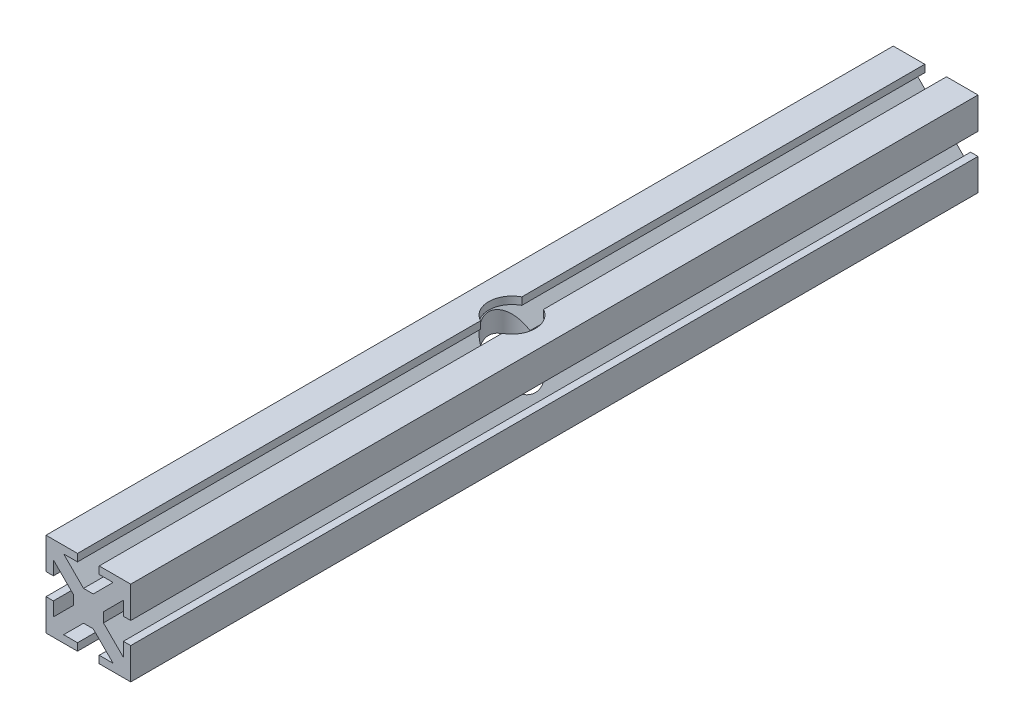
SolidWorks part; units mm, degrees
ref_plane "Front Plane" through (0, 0, 0) normal (0, 0, 1) x (1, 0, 0)
ref_plane "Top Plane" through (0, 0, 0) normal (0, 1, 0) x (1, 0, 0)
ref_plane "Right Plane" through (0, 0, 0) normal (1, 0, 0) x (0, 0, -1)
sketch "Sketch1" plane through (0, 0, 0) normal (0, 0, 1) x (1, 0, 0)
  line L1 (-12.7, -12.7) -> (12.7, -12.7)
  line L2 (-12.7, -12.7) -> (-12.7, 12.7)
  line L3 (-12.7, 12.7) -> (12.7, 12.7)
  line L4 (12.7, -12.7) -> (12.7, 12.7)
  line L5 (-12.7, -12.7) -> (12.7, 12.7) construction
  line L6 (-12.7, 12.7) -> (12.7, -12.7) construction
  point P0 (0, 0)
extrude "Boss-Extrude2" add sketch "Sketch1" along normal blind 254 contours L3 L4 L1 L2
sketch "Sketch3" plane through (0, 0, 254) normal (0, 0, 1) x (1, 0, 0)
  line L0 (-4.5212, 4.5212) -> (-12.7, 12.7)
  line L1 (-4.5212, 4.5212) -> (4.5212, 4.5212)
  line L2 (-4.5212, 4.5212) -> (-4.5212, -4.5212)
  line L3 (-4.5212, -4.5212) -> (4.5212, -4.5212)
  line L4 (4.5212, 4.5212) -> (4.5212, -4.5212)
  line L5 (-4.5212, 4.5212) -> (4.5212, -4.5212) construction
  line L6 (-4.5212, -4.5212) -> (4.5212, 4.5212) construction
  line L7 (0, 12.7) -> (-3.2512, 12.7)
  line L8 (-12.7, 12.7) -> (12.7, 12.7) construction
  line L9 (-3.2512, 12.7) -> (-3.2512, 10.4902)
  line L10 (-3.2512, 10.4902) -> (-7.4172, 10.4902)
  line L11 (-7.4172, 10.4902) -> (-1.4482, 4.5212)
  line L12 (3.2512, 12.7) -> (-3.2512, 12.7)
  line L13 (7.4172, 10.4902) -> (1.4482, 4.5212)
  line L14 (3.2512, 10.4902) -> (7.4172, 10.4902)
  line L15 (3.2512, 12.7) -> (3.2512, 10.4902)
  line L16 (-10.4902, 7.4172) -> (-4.5212, 1.4482)
  line L17 (-10.4902, 3.2512) -> (-10.4902, 7.4172)
  line L18 (-12.7, 3.2512) -> (-10.4902, 3.2512)
  line L19 (12.7, 3.2512) -> (10.4902, 3.2512)
  line L20 (10.4902, 3.2512) -> (10.4902, 7.4172)
  line L21 (10.4902, 7.4172) -> (4.5212, 1.4482)
  line L22 (-12.7, 3.2512) -> (-12.7, -3.2512)
  line L24 (12.7, -3.2512) -> (10.4902, -3.2512)
  line L25 (10.4902, -3.2512) -> (10.4902, -7.4172)
  line L26 (10.4902, -7.4172) -> (4.5212, -1.4482)
  line L27 (3.2512, -12.7) -> (3.2512, -10.4902)
  line L28 (3.2512, -10.4902) -> (7.4172, -10.4902)
  line L29 (7.4172, -10.4902) -> (1.4482, -4.5212)
  line L30 (-3.2512, -12.7) -> (-3.2512, -10.4902)
  line L31 (-3.2512, -10.4902) -> (-7.4172, -10.4902)
  line L32 (-7.4172, -10.4902) -> (-1.4482, -4.5212)
  line L33 (-12.7, -3.2512) -> (-10.4902, -3.2512)
  line L34 (-10.4902, -3.2512) -> (-10.4902, -7.4172)
  line L35 (-10.4902, -7.4172) -> (-4.5212, -1.4482)
  line L36 (-12.7, -3.2512) -> (-12.7, -12.7)
  line L37 (-12.7, -12.7) -> (-3.2512, -12.7)
  line L38 (3.2512, -12.7) -> (12.7, -12.7)
  line L39 (12.7, -12.7) -> (12.7, -3.2512)
  line L40 (12.7, 3.2512) -> (12.7, 12.7)
  line L41 (12.7, 12.7) -> (3.2512, 12.7)
  line L42 (-3.2512, 12.7) -> (-12.7, 12.7)
  line L43 (-12.7, 12.7) -> (-12.7, 3.2512)
  line L44 (-3.2512, -12.7) -> (3.2512, -12.7)
  line L45 (12.7, -3.2512) -> (12.7, 3.2512)
  point P0 (0, 0)
  line M20 (-12.7, 12.7) -> (-12.7, -12.7)
  line M21 (-12.7, -12.7) -> (12.7, -12.7)
  line M22 (12.7, -12.7) -> (12.7, 12.7)
  line M23 (12.7, 12.7) -> (-12.7, 12.7)
extrude "Cut-Extrude1" cut sketch "Sketch3" against normal blind 254 contours L34 L35 L2 L16 L17 L18 L33 M20 | L15 L9 L10 L11 L1 L13 L14 M23 | L26 L25 L24 L19 L20 L21 L4 M22 | L32 L31 L30 L27 L28 L29 L3 M21
sketch "Sketch5" plane through (0, 12.7, 0) normal (0, 1, 0) x (1, 0, 0)
  line L0 (-12.7, 0) -> (-12.7, -127)
  line L1 (-12.7, -254) -> (-12.7, 0) construction
  line L2 (-12.7, -127) -> (12.7, -127)
  line L3 (12.7, -254) -> (12.7, 0) construction
  circle A0 centre (0, -127) radius 7
  line M1 (-3.2512, -254) -> (-3.2512, 0)
extrude "Cut-Extrude2" cut sketch "Sketch5" against normal blind 250 contours A0 L2 M1 | L2 A0 M1 | A0 L2 M1 | L2 A0 M1
